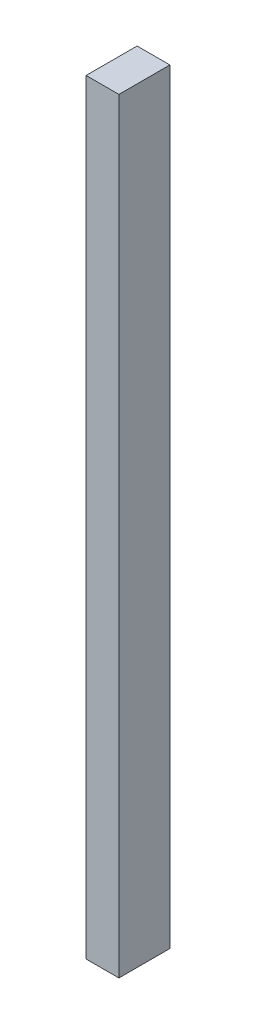
SolidWorks part; units mm, degrees
material "Pine"
ref_plane "Front Plane" through (0, 0, 0) normal (0, 0, 1) x (1, 0, 0)
ref_plane "Top Plane" through (0, 0, 0) normal (0, 1, 0) x (1, 0, 0)
ref_plane "Right Plane" through (0, 0, 0) normal (1, 0, 0) x (0, 0, -1)
sketch "Sketch1" plane through (0, 0, 0) normal (0, 1, 0) x (1, 0, 0)
  line L1 (0, 0) -> (45, 0)
  line L2 (0, 0) -> (0, 70)
  line L3 (0, 70) -> (45, 70)
  line L4 (45, 0) -> (45, 70)
  dimension "D1" = 70
  dimension "D2" = 45
extrude "Boss-Extrude1" add sketch "Sketch1" along normal blind 1050
